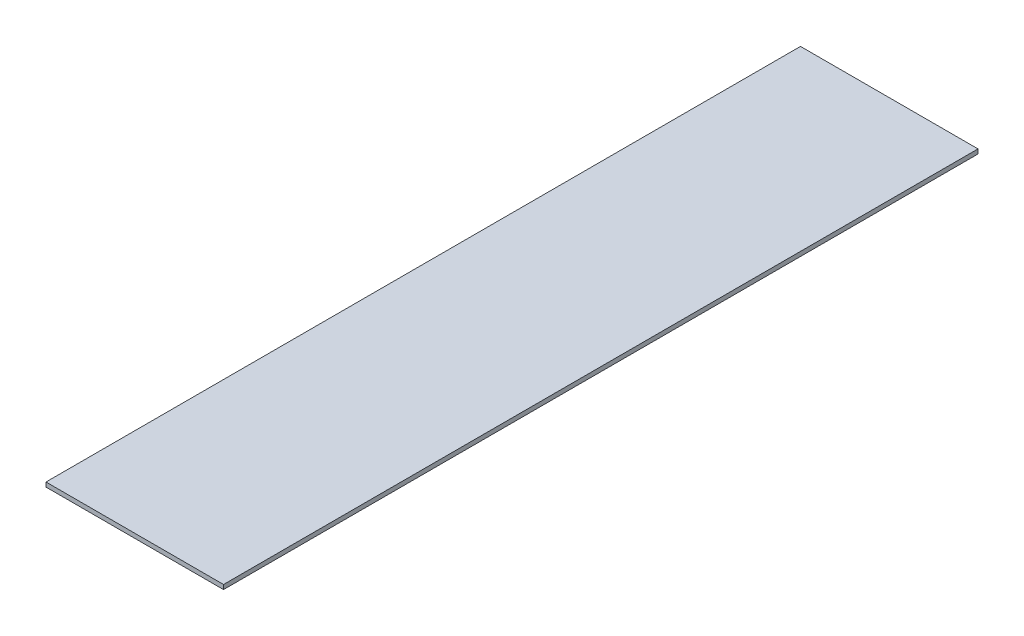
SolidWorks part; units mm, degrees
ref_plane "Face" through (0, 0, 0) normal (0, 0, 1) x (1, 0, 0)
ref_plane "Dessus" through (0, 0, 0) normal (0, 1, 0) x (1, 0, 0)
ref_plane "Droite" through (0, 0, 0) normal (1, 0, 0) x (0, 0, -1)
sketch "Esquisse1" plane through (0, 0, 0) normal (0, 1, 0) x (1, 0, 0)
  line L1 (0, 0) -> (400, 0)
  line L2 (0, 0) -> (0, 1700)
  line L3 (0, 1700) -> (400, 1700)
  line L4 (400, 0) -> (400, 1700)
  dimension "D1" = 1700
  dimension "D2" = 400
extrude "Extrusion1" add sketch "Esquisse1" along normal blind 10
